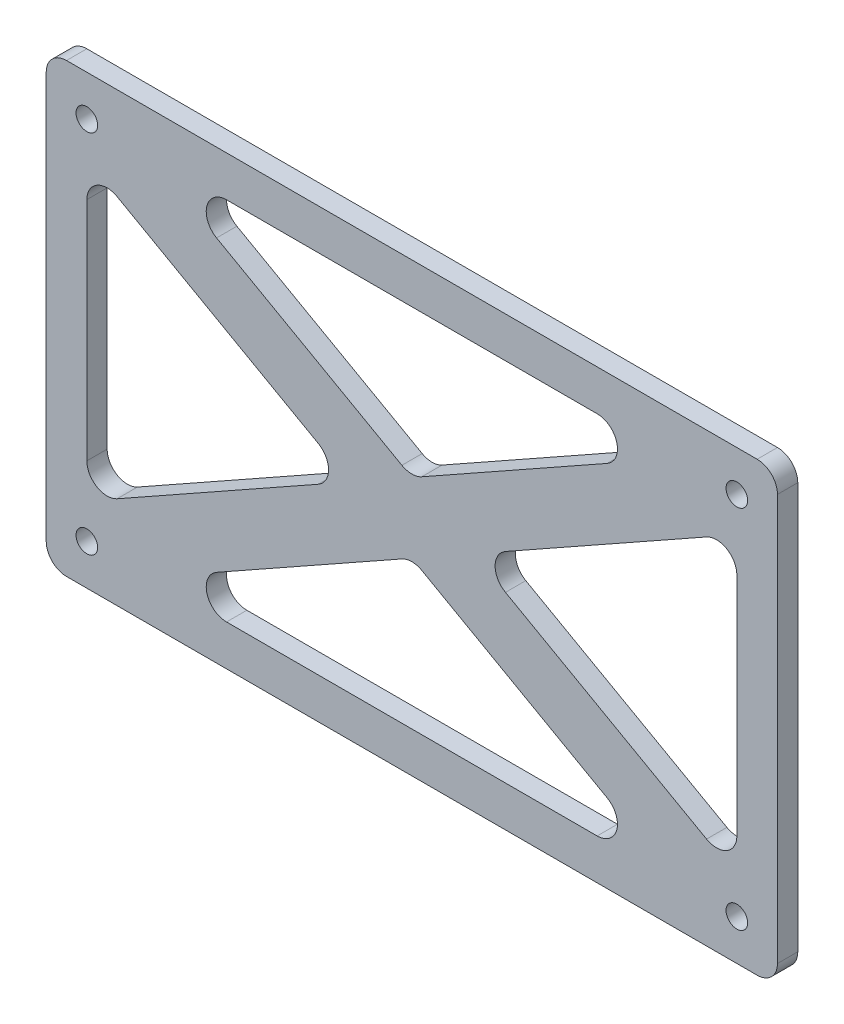
SolidWorks part; units mm, degrees
ref_plane "Front Plane" through (0, 0, 0) normal (0, 0, 1) x (1, 0, 0)
ref_plane "Top Plane" through (0, 0, 0) normal (0, 1, 0) x (1, 0, 0)
ref_plane "Right Plane" through (0, 0, 0) normal (1, 0, 0) x (0, 0, -1)
sketch "Sketch1" plane through (0, 0, 0) normal (0, 0, 1) x (1, 0, 0)
  line L0 (114.3, 69.85) -> (-114.3, 69.85)
  line L1 (101.6, 57.15) -> (-101.6, 57.15)
  line L2 (101.6, 57.15) -> (101.6, -57.15)
  line L3 (101.6, -57.15) -> (-101.6, -57.15)
  line L4 (-101.6, 57.15) -> (-101.6, -57.15)
  line L5 (101.6, 57.15) -> (-101.6, -57.15) construction
  line L6 (101.6, -57.15) -> (-101.6, 57.15) construction
  line L7 (-114.3, 69.85) -> (-114.3, -69.85)
  line L8 (114.3, -69.85) -> (-114.3, -69.85)
  line L9 (114.3, 69.85) -> (114.3, -69.85)
  point P0 (0, 0)
  dimension "D1" = 203.2
  dimension "D2" = 114.3
  dimension "D3" = 12.7
extrude "Boss-Extrude1" add sketch "Sketch1" along normal blind 6.35
sketch "Sketch2" plane through (0, 0, 6.35) normal (0, 0, 1) x (1, 0, 0)
  line L0 (-101.6, 57.15) -> (101.6, -57.15) construction
  line L1 (-101.6, -57.15) -> (101.6, 57.15) construction
  line L2 (-96.9303, 65.4518) -> (0, 10.9285)
  line L3 (-106.2697, -48.8482) -> (-19.4284, 0)
  line L4 (-106.2697, 48.8482) -> (-19.4284, 0)
  line L5 (-96.9303, -65.4518) -> (0, -10.9285)
  line L6 (0, 10.9285) -> (96.9303, 65.4518)
  line L7 (0, -10.9285) -> (96.9303, -65.4518)
  line L8 (-106.2697, -48.8482) -> (96.9303, 65.4518) construction
  line L9 (19.4284, 0) -> (106.2697, 48.8482)
  line L10 (-106.2697, 48.8482) -> (96.9303, -65.4518) construction
  line L11 (19.4284, 0) -> (106.2697, -48.8482)
  line L12 (-96.9303, -65.4518) -> (106.2697, 48.8482) construction
  line L14 (-96.9303, 65.4518) -> (106.2697, -48.8482) construction
  arc A0 (-96.9303, 65.4518) -> (-106.2697, 48.8482) centre (-101.6, 57.15) ccw
  arc A1 (106.2697, -48.8482) -> (96.9303, -65.4518) centre (101.6, -57.15) cw
  arc A2 (-106.2697, -48.8482) -> (-96.9303, -65.4518) centre (-101.6, -57.15) ccw
  arc A3 (96.9303, 65.4518) -> (106.2697, 48.8482) centre (101.6, 57.15) cw
  dimension "D1" = 9.525
  dimension "D2" = 9.525
extrude "Boss-Extrude2" add sketch "Sketch2" against normal blind 6.35
fillet "Fillet1" radius 6.35 12 edges at (-82.1716, 57.15, 3.175) (0, 10.9285, 3.175) (82.1716, 57.15, 3.175) (101.6, 46.2215, 3.175) (101.6, -46.2215, 3.175) (19.4284, 0, 3.175) (0, -10.9285, 3.175) (82.1716, -57.15, 3.175) (-82.1716, -57.15, 3.175) (-101.6, -46.2215, 3.175) (-19.4284, 0, 3.175) (-101.6, 46.2215, 3.175)
fillet "Fillet2" radius 6.35 4 edges at (114.3, 69.85, 3.175) (114.3, -69.85, 3.175) (-114.3, -69.85, 3.175) (-114.3, 69.85, 3.175)
hole_wizard "1/4 Clearance Hole1" positions "Sketch4" profile "Sketch3" hole size "1/4" standard "Ansi Inch"
sketch "Sketch4" plane through (0, 0, 6.35) normal (0, 0, 1) x (1, 0, 0)
  line L1 (101.6, 57.15) -> (-101.6, 57.15)
  line L2 (101.6, 57.15) -> (101.6, -57.15)
  line L3 (101.6, -57.15) -> (-101.6, -57.15)
  line L4 (-101.6, 57.15) -> (-101.6, -57.15)
  line L5 (101.6, 57.15) -> (-101.6, -57.15) construction
  line L6 (101.6, -57.15) -> (-101.6, 57.15) construction
  point P0 (-101.6, 57.15)
  point P1 (101.6, 57.15)
  point P3 (-101.6, -57.15)
  point P5 (101.6, -57.15)
  dimension "D1" = 203.2
  dimension "D2" = 114.3
sketch "Sketch3" plane through (-101.6, 57.15, 6.35) normal (1, 0, 0) x (0, -1, 0)
  line L0 (0, 0) -> (0, 11.9358)
  line L1 (0, 11.9358) -> (3.3782, 9.906)
  line L2 (3.3782, 9.906) -> (3.3782, 0)
  line L5 (3.3782, 0) -> (0, 0)
  line L10 (0, 11.9358) -> (-3.3782, 9.906) construction
  line L11 (0, -6.35) -> (0, 107.95) construction
  dimension "Hole Dia." = 6.7564
  dimension "Hole Depth" = 9.906
  dimension "Drill Angle" = 118
